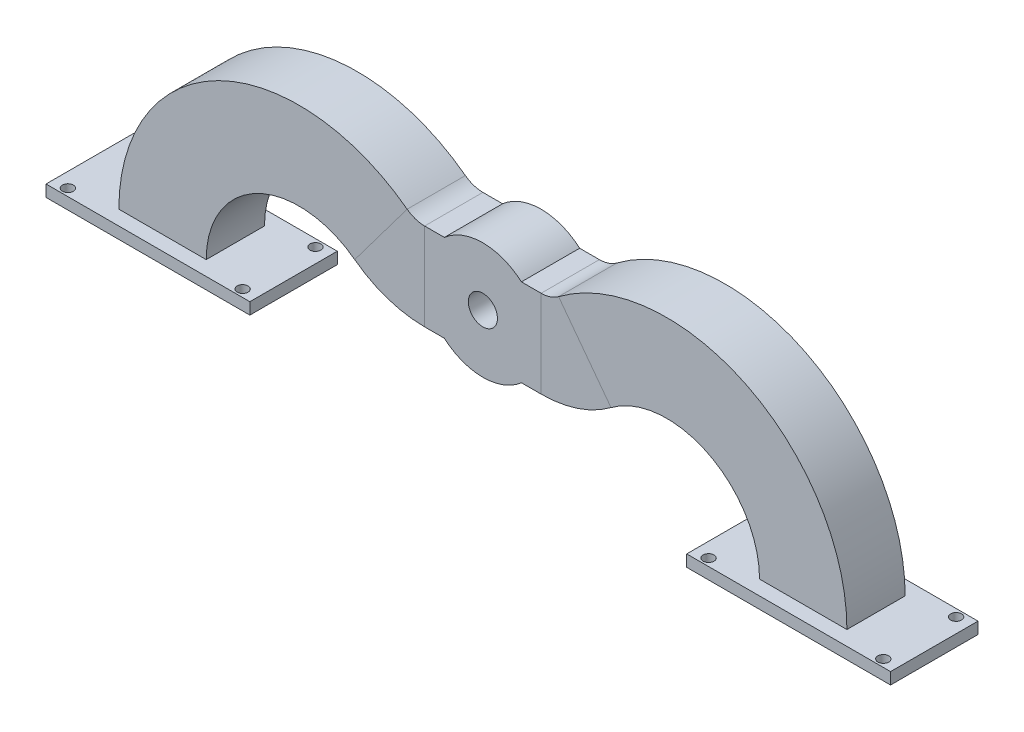
SolidWorks part; units mm, degrees
ref_plane "Front Plane" through (0, 0, 0) normal (0, 0, 1) x (1, 0, 0)
ref_plane "Top Plane" through (0, 0, 0) normal (0, 1, 0) x (1, 0, 0)
ref_plane "Right Plane" through (0, 0, 0) normal (1, 0, 0) x (0, 0, -1)
sketch "Sketch1" plane through (0, 0, 0) normal (0, 0, 1) x (1, 0, 0)
  circle A0 centre (0, 0) radius 5
  circle A1 centre (0, 0) radius 20
  dimension "D1" = 10
  dimension "D2" = 40
extrude "Boss-Extrude1" add sketch "Sketch1" along normal blind 20
sketch "Sketch2" plane through (0, 0, 0) normal (0, 0, 1) x (1, 0, 0)
  line L0 (0, 0) -> (-20, 0)
  line L1 (-110, -32.5) -> (-110, -19.7946) construction
  circle A0 centre (0, 0) radius 20 construction
  arc A1 (-20, 0) -> (-35, 5) centre (-20, 25) cw
  arc A2 (-35, 5) -> (-110, -32.5) centre (-63.125, -32.5) ccw
  dimension "D1" = 90
  dimension "D2" = 5
  dimension "D3" = 15
sketch "Sketch3" plane through (0, 0, 0) normal (1, 0, 0) x (0, 0, -1)
  line L0 (0, -20) -> (0, 20) construction
  line L1 (-20, 15) -> (0, 15)
  line L2 (-20, 15) -> (-20, -15)
  line L3 (-20, -15) -> (0, -15)
  line L4 (0, 15) -> (0, -15)
  line L5 (-20, 15) -> (0, -15) construction
  line L6 (-20, -15) -> (0, 15) construction
  line L8 (-17.5, 10) -> (-2.5, 10)
  line L9 (-17.5, 10) -> (-17.5, -10)
  line L10 (-17.5, -10) -> (-2.5, -10)
  line L11 (-2.5, 10) -> (-2.5, -10)
  line L12 (-17.5, 10) -> (-2.5, -10) construction
  line L13 (-17.5, -10) -> (-2.5, 10) construction
  point P0 (-10, 0)
  point P7 (-10, 0)
  dimension "D1" = 10
  dimension "D2" = 20
  dimension "D3" = 30
  dimension "D4" = 20
  dimension "D5" = 15
sweep "Sweep1" add profiles "Sketch3" path "Sketch2"
mirror "Mirror1" about plane through (0, 0, 0) normal (1, 0, 0) of bodies 102
sketch "Sketch4" plane through (0, 0, 20) normal (0, 0, 1) x (1, 0, 0)
  circle A0 centre (0, 0) radius 5
  dimension "D1" = 10
extrude "Cut-Extrude1" cut sketch "Sketch4" against normal through all both and the other way through all
sketch "Sketch5" plane through (0, 0, 0) normal (0, 0, -1) x (-1, 0, 0)
  line L0 (0, 0) -> (0, -24.7267) construction
  circle A0 centre (-25, 0) radius 10
  circle A1 centre (25, 0) radius 10
  dimension "D2" = 20
  dimension "D1" = 25
extrude "Cut-Extrude2" cut sketch "Sketch5" against normal blind 17.5 and the other way through all
sketch "Sketch6" plane through (0, -32.5, 0) normal (0, -1, 0) x (1, 0, 0)
  line L0 (110, 25.0132) -> (110, 10) construction
  line L1 (75, 25.0132) -> (145, 25.0132)
  line L2 (75, 25.0132) -> (75, -5.0132)
  line L3 (75, -5.0132) -> (145, -5.0132)
  line L4 (145, 25.0132) -> (145, -5.0132)
  line L5 (75, 25.0132) -> (145, -5.0132) construction
  line L6 (75, -5.0132) -> (145, 25.0132) construction
  line L7 (110, 10) -> (75, 10) construction
  line L11 (100, 17.5) -> (120, 17.5)
  line L12 (100, 17.5) -> (100, 2.5)
  line L13 (100, 2.5) -> (120, 2.5)
  line L14 (120, 17.5) -> (120, 2.5)
  circle A0 centre (80, 22.5) radius 1.8681
  circle A1 centre (140, 22.5) radius 1.8681
  circle A2 centre (140, -2.5) radius 1.8681
  circle A3 centre (80, -2.5) radius 1.8681
  point P0 (110, 10)
  point P12 (110, 2.5)
  dimension "D1" = 30.0265
  dimension "D2" = 70
  dimension "D3" = 30
  dimension "D4" = 12.5
extrude "Boss-Extrude2" add sketch "Sketch6" along normal blind 4
mirror "Mirror2" about plane through (0, 0, 0) normal (1, 0, 0) of bodies 106
